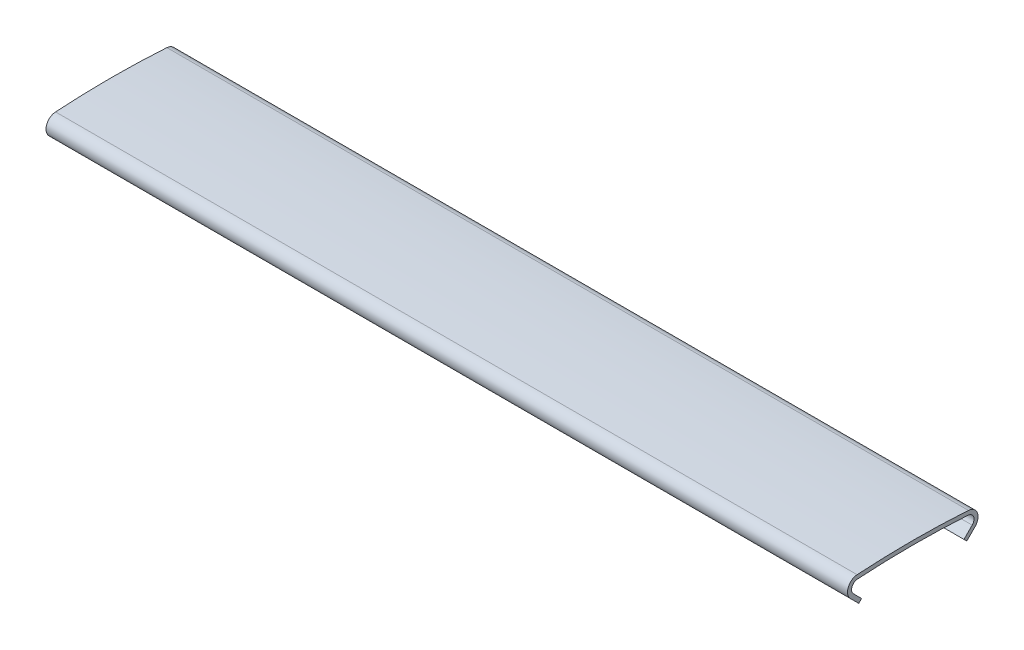
SolidWorks part; units mm, degrees
material "Acrylic (Medium-high impact)"
ref_plane "Front Plane" through (0, 0, 0) normal (0, 0, 1) x (1, 0, 0)
ref_plane "Top Plane" through (0, 0, 0) normal (0, 1, 0) x (1, 0, 0)
ref_plane "Right Plane" through (0, 0, 0) normal (1, 0, 0) x (0, 0, -1)
sketch "Sketch1" plane through (0, 0, 0) normal (1, 0, 0) x (0, 0, -1)
  line L0 (0, -92.14) -> (-5.9727, -0.1938) construction
  line L1 (0, -92.14) -> (5.9727, -0.1938) construction
  line L2 (-5.9727, -0.1938) -> (0, -0.1938) construction
  line L3 (0, -92.14) -> (0, 0) construction
  line L4 (0, -0.1938) -> (5.9727, -0.1938) construction
  line L5 (5.9015, -1.29) -> (6.6782, -2.0668) construction
  line L6 (-5.9015, -1.29) -> (-6.6782, -2.0668) construction
  line L7 (6.6782, -2.0668) -> (5.7935, -2.9515)
  line L8 (-6.07, -0.79) -> (6.07, -0.79) construction
  line L9 (-6.6782, -2.0668) -> (-5.7935, -2.9515)
  line L10 (-7, -2.9515) -> (7, -2.9515) construction
  line L11 (-7, -2.9515) -> (-7, 0) construction
  line L12 (-7, 0) -> (7, 0) construction
  line L13 (7, -2.9515) -> (7, 0) construction
  line L14 (-5.7935, -2.9515) -> (-5.4895, -2.6474)
  line L15 (-5.4895, -2.6474) -> (-6.3742, -1.7627)
  line L16 (5.7935, -2.9515) -> (5.4895, -2.6474)
  line L17 (5.4895, -2.6474) -> (6.3742, -1.7627)
  line L18 (-6.4028, -1.6632) -> (-4.3413, -3.5017) construction
  line L19 (6.4028, -1.6632) -> (4.3413, -3.5017) construction
  line L20 (-4.3413, -3.5017) -> (4.3413, -3.5017) construction
  line L21 (0, -3.5017) -> (0, -0.79) construction
  arc A0 (5.9727, -0.1938) -> (-5.9727, -0.1938) centre (0, -92.14) ccw
  arc A1 (5.9448, -0.6229) -> (-5.9448, -0.6229) centre (0, -92.14) ccw
  arc A2 (-5.9727, -0.1938) -> (-6.6782, -2.0668) centre (-5.9015, -1.29) ccw
  arc A3 (-5.9448, -0.6229) -> (-6.3742, -1.7627) centre (-5.9015, -1.29) ccw
  arc A4 (6.6782, -2.0668) -> (5.9727, -0.1938) centre (5.9015, -1.29) ccw
  arc A5 (6.3742, -1.7627) -> (5.9448, -0.6229) centre (5.9015, -1.29) ccw
  arc A6 (6.07, -0.79) -> (6.4028, -1.6632) centre (6.07, -1.29) cw construction
  arc A7 (-6.07, -0.79) -> (-6.4028, -1.6632) centre (-6.07, -1.29) ccw construction
  dimension "D1" = 0.43
  dimension "D8" = 0.5
  dimension "D2" = 14
  dimension "D3" = 0.79
  dimension "D6" = 41.728
  dimension "D9" = 12.14
extrude "Boss-Extrude1" add sketch "Sketch1" along normal mid plane 86
